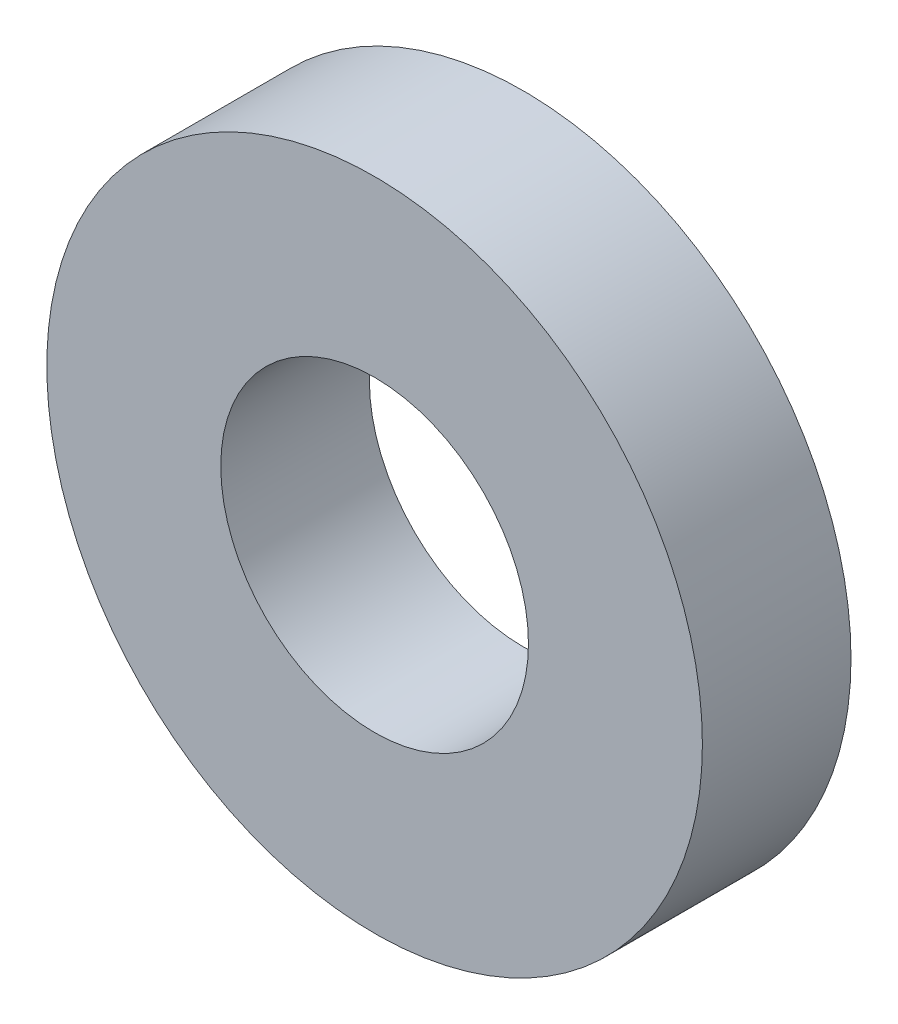
SolidWorks part; units mm, degrees
ref_plane "Front Plane" through (0, 0, 0) normal (0, 0, 1) x (1, 0, 0)
ref_plane "Top Plane" through (0, 0, 0) normal (0, 1, 0) x (1, 0, 0)
ref_plane "Right Plane" through (0, 0, 0) normal (1, 0, 0) x (0, 0, -1)
sketch "Çizim1" plane through (0, 0, 0) normal (0, 0, 1) x (1, 0, 0)
  circle A0 centre (0, 0) radius 37.5
  circle A1 centre (0, 0) radius 17.6
  dimension "D1" = 75
  dimension "D2" = 35.2
extrude "Yükseklik-Ekstrüzyon1" add sketch "Çizim1" along normal mid plane 17
